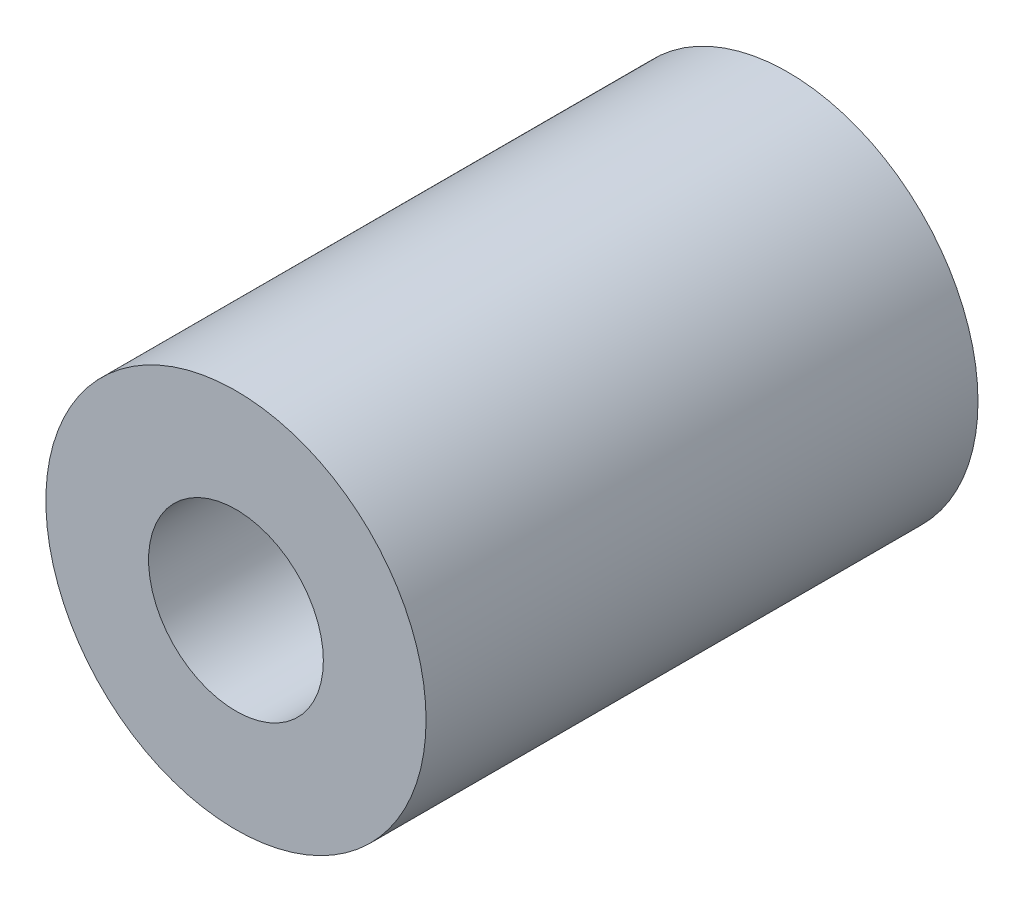
SolidWorks part; units mm, degrees
ref_plane "Front Plane" through (0, 0, 0) normal (0, 0, 1) x (1, 0, 0)
ref_plane "Top Plane" through (0, 0, 0) normal (0, 1, 0) x (1, 0, 0)
ref_plane "Right Plane" through (0, 0, 0) normal (1, 0, 0) x (0, 0, -1)
sketch "Sketch1" plane through (0, 0, 0) normal (0, 0, 1) x (1, 0, 0)
  circle A0 centre (0, 0) radius 1.425
  circle A1 centre (0, 0) radius 3.1
  dimension "D1" = 6.2
  dimension "D2" = 2.85
extrude "Boss-Extrude1" add sketch "Sketch1" along normal blind 9
